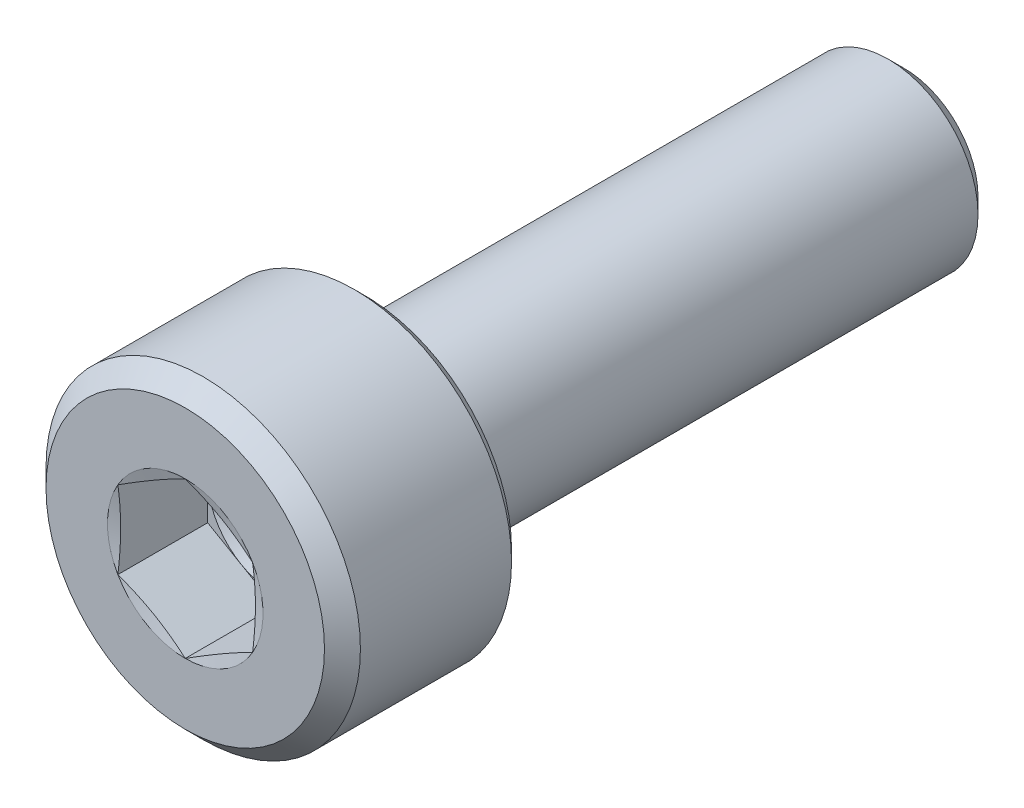
SolidWorks part; units mm, degrees
ref_plane "Front Plane" through (0, 0, 0) normal (0, 0, 1) x (1, 0, 0)
ref_plane "Top Plane" through (0, 0, 0) normal (0, 1, 0) x (1, 0, 0)
ref_plane "Right Plane" through (0, 0, 0) normal (1, 0, 0) x (0, 0, -1)
sketch "Sketch1" plane through (0, 0, 0) normal (1, 0, 0) x (0, 0, -1)
  line L0 (0, 0) -> (12.9407, 0) construction
  line L1 (0, 0) -> (0, 3.1)
  line L2 (0, 3.1) -> (0.4, 3.5)
  line L3 (0.4, 3.5) -> (3.765, 3.5)
  line L4 (4, 3.265) -> (4, 2.35)
  line L5 (4.6, 2) -> (15.65, 2)
  line L6 (15.65, 2) -> (16, 1.65)
  line L7 (16, 1.65) -> (16, 0)
  line L8 (16, 0) -> (0, 0)
  line L9 (3.765, 3.5) -> (4, 3.265)
  line L10 (4.5298, 2.0127) -> (4.1298, 2.1627)
  arc A2 (4.6, 2) -> (4.5298, 2.0127) centre (4.6, 2.2) cw
  arc A3 (4.1298, 2.1627) -> (4, 2.35) centre (4.2, 2.35) cw
  point P6 (4, 3.5)
  dimension "R2" = 0.2
  dimension "R1" = 0.2
  dimension "D1" = 45
  dimension "DK" = 7
  dimension "D3" = 45
  dimension "length" = 12
  dimension "K" = 4
  dimension "V" = 0.4
  dimension "HOLESIZE" = 4
  dimension "D4" = 3.3
  dimension "D5" = 45
  dimension "DW" = 6.53
  dimension "F" = 0.6
  dimension "DA" = 4.7
revolve "Revolve1" add sketch "Sketch1" angle 360 about L0
cosmetic thread "Cosmetic Thread1" parameters "D1"=9.9, "D2"=4
sketch "Sketch2" plane through (0, 0, 0) normal (0, 0, 1) x (1, 0, 0)
  line L0 (0, 0) -> (0, 1.7321) construction
  line L2 (0, 1.7321) -> (-1.5, 0.866)
  line L3 (-1.5, 0.866) -> (-1.5, -0.866)
  line L4 (-1.5, -0.866) -> (0, -1.7321)
  line L5 (0, -1.7321) -> (1.5, -0.866)
  line L6 (1.5, -0.866) -> (1.5, 0.866)
  line L7 (1.5, 0.866) -> (0, 1.7321)
  circle A0 centre (0, 0) radius 1.5 construction
  dimension "S" = 3
extrude "Cut-Extrude1" cut sketch "Sketch2" against normal blind 2
sketch "Sketch3" plane through (0, 0, 0) normal (1, 0, 0) x (0, 0, -1)
  line L0 (2, 0) -> (16, 0) construction
  line L1 (16, -1.65) -> (16, 1.65) construction
  line L2 (2, 0) -> (2, 1.5)
  line L4 (2, 1.5) -> (2.866, 0)
  line L5 (2.866, 0) -> (2, 0)
  line L6 (0, 3.1) -> (0, -3.1) construction
  dimension "DRILLANG" = 60
  dimension "DRILL DEPTH" = 2
  dimension "S2" = 3
revolve "Cut-Revolve2" cut sketch "Sketch3" angle 360 about L0
sketch "Sketch4" plane through (0, 0, 0) normal (1, 0, 0) x (0, 0, -1)
  line L0 (0, 0) -> (4.6121, 0) construction
  line L1 (0, 1.7321) -> (0, 1.5)
  line L2 (0, 3.1) -> (0, -3.1) construction
  line L3 (0, 1.5) -> (0.0622, 1.5)
  line L4 (0.0622, 1.5) -> (0, 1.7321)
  point P12 (0.0311, 1.5)
  dimension "D1" = 3
  dimension "D2" = 15
revolve "Cut-Revolve3" cut sketch "Sketch4" angle 360 about L0
